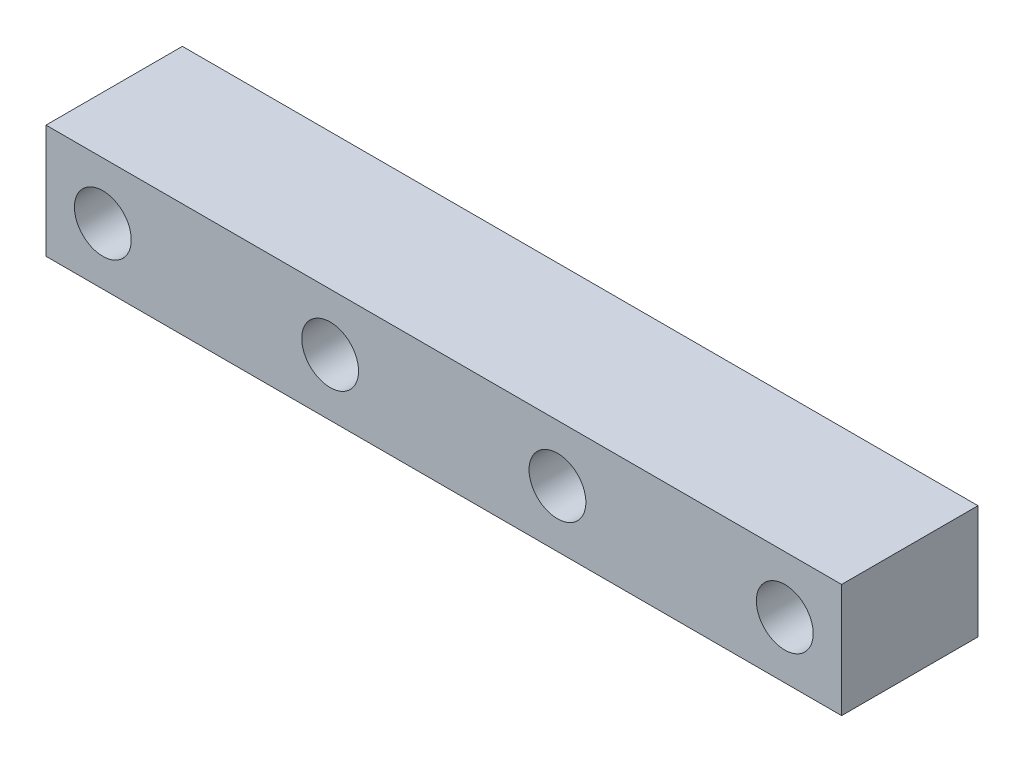
SolidWorks part; units mm, degrees
ref_plane "Front Plane" through (0, 0, 0) normal (0, 0, 1) x (1, 0, 0)
ref_plane "Top Plane" through (0, 0, 0) normal (0, 1, 0) x (1, 0, 0)
ref_plane "Right Plane" through (0, 0, 0) normal (1, 0, 0) x (0, 0, -1)
sketch "Sketch2" plane through (0, 0, 0) normal (0, 0, 1) x (1, 0, 0)
  line L1 (-22.225, -3.175) -> (22.225, -3.175)
  line L2 (-22.225, -3.175) -> (-22.225, 3.175)
  line L3 (-22.225, 3.175) -> (22.225, 3.175)
  line L4 (22.225, -3.175) -> (22.225, 3.175)
  line L5 (-22.225, -3.175) -> (22.225, 3.175) construction
  line L6 (-22.225, 3.175) -> (22.225, -3.175) construction
  point P0 (0, 0)
  dimension "D1" = 44.45
  dimension "D2" = 6.35
extrude "Boss-Extrude1" add sketch "Sketch2" along normal blind 7.62
sketch "Sketch4" plane through (0, 0, 0) normal (0, 0, -1) x (-1, 0, 0)
  line L0 (0, 3.175) -> (0, -3.175) construction
  line L1 (-22.225, 3.175) -> (22.225, 3.175) construction
  line L2 (22.225, -3.175) -> (-22.225, -3.175) construction
  line L3 (-22.225, 0) -> (22.225, 0) construction
  line L4 (-22.225, -3.175) -> (-22.225, 3.175) construction
  line L5 (22.225, 3.175) -> (22.225, -3.175) construction
  circle A0 centre (-6.35, 0) radius 1.5875
  circle A1 centre (-19.05, 0) radius 1.5875
  point P16 (-4.8968, 0)
  dimension "D1" = 3.175
  dimension "D2" = 3.175
  dimension "D3" = 12.7
  dimension "D4" = 12.7
extrude "Cut-Extrude2" cut sketch "Sketch4" against normal through all
mirror "Mirror2" about plane through (0, 0, 0) normal (1, 0, 0) of "Cut-Extrude2"
